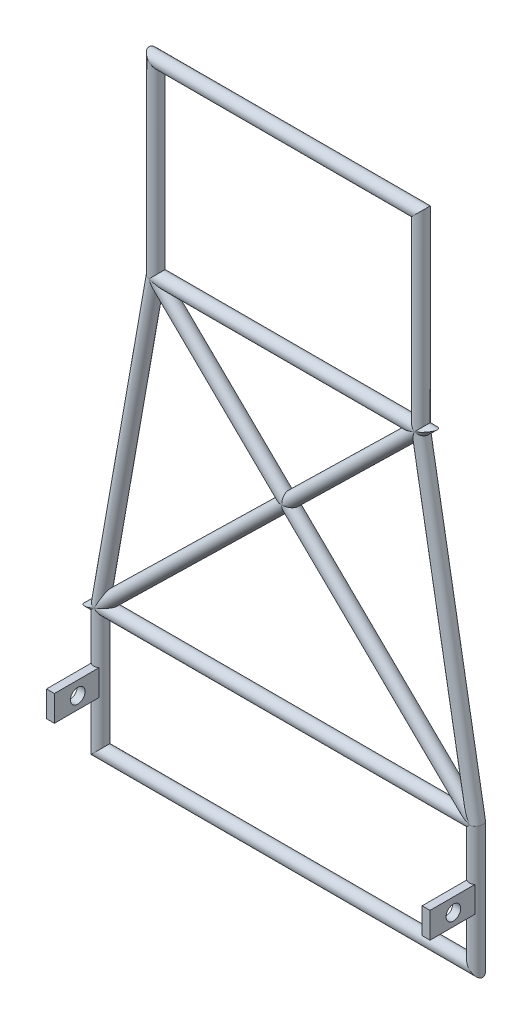
SolidWorks part; units mm, degrees
ref_plane "Front Plane" through (0, 0, 0) normal (0, 0, 1) x (1, 0, 0)
ref_plane "Top Plane" through (0, 0, 0) normal (0, 1, 0) x (1, 0, 0)
ref_plane "Right Plane" through (0, 0, 0) normal (1, 0, 0) x (0, 0, -1)
sketch "Sketch1" plane through (0, 0, 0) normal (0, 0, 1) x (1, 0, 0)
  line L0 (-211.8365, 700) -> (211.8365, 700)
  line L1 (-300, 0) -> (300, 0)
  line L2 (300, 0) -> (300, 200)
  line L3 (-300, 200) -> (211.8365, 700)
  line L4 (300, 200) -> (211.8365, 700)
  line L5 (211.8365, 700) -> (211.8365, 1000)
  line L6 (211.8365, 1000) -> (-211.8365, 1000)
  line L7 (-300, 0) -> (-300, 200)
  line L8 (-300, 200) -> (-211.8365, 700)
  line L9 (-211.8365, 700) -> (-211.8365, 1000)
  line L10 (300, 200) -> (-211.8365, 700)
  line L11 (-300, 200) -> (300, 200)
  dimension "D3" = 200
  dimension "D5" = 300
other "Pipe - configured 21.3 X 2.3(1)"
ref_plane "Plane1" through (-211.8365, 700, 0) normal (0, 1, 0) x (-1, 0, 0)
sketch "Sketch11" plane through (-211.8365, 700, 0) normal (0, 1, 0) x (-1, 0, 0)
  circle A0 centre (0, 0) radius 8.35
  circle A1 centre (0, 0) radius 10.65
  point P3 (0, 10.65)
  point P5 (-10.65, 0)
  point P6 (0, -10.65)
  point P7 (10.65, 0)
  point P8 (0, 0)
  dimension "In_dia" = 16.7
  dimension "Out_dia" = 21.3
other "Pipe - configured 21.3 X 2.3(2)"
ref_plane "Plane2" through (-211.8365, 700, 0) normal (1, 0, 0) x (0, 1, 0)
sketch "Sketch12" plane through (-211.8365, 700, 0) normal (1, 0, 0) x (0, 1, 0)
  circle A0 centre (0, 0) radius 8.35
  circle A1 centre (0, 0) radius 10.65
  point P3 (0, 10.65)
  point P5 (-10.65, 0)
  point P6 (0, -10.65)
  point P7 (10.65, 0)
  point P8 (0, 0)
  dimension "In_dia" = 16.7
  dimension "Out_dia" = 21.3
other "Pipe - configured 21.3 X 2.3(3)"
ref_plane "Plane3" through (300, 200, 0) normal (-0.7153, 0.6988, 0) x (-0.6988, -0.7153, 0)
sketch "Sketch13" plane through (300, 200, 0) normal (-0.7153, 0.6988, 0) x (-0.6988, -0.7153, 0)
  circle A0 centre (0, 0) radius 8.35
  circle A1 centre (0, 0) radius 10.65
  point P3 (0, 10.65)
  point P5 (-10.65, 0)
  point P6 (0, -10.65)
  point P7 (10.65, 0)
  point P8 (0, 0)
  dimension "In_dia" = 16.7
  dimension "Out_dia" = 21.3
sketch "Sketch14" plane through (0, 0, 0) normal (0, 0, 1) x (1, 0, 0)
  line L0 (0, 0) -> (0, 305.8859) construction
  line L1 (306.3871, 78.6524) -> (293.747, 78.6524)
  line L2 (-306.3871, 119.9433) -> (-293.747, 119.9433)
  line L3 (-306.3871, 119.9433) -> (-306.3871, 78.6524)
  line L4 (-306.3871, 78.6524) -> (-293.747, 78.6524)
  line L5 (-293.747, 119.9433) -> (-293.747, 78.6524)
  line L6 (306.3871, 119.9433) -> (306.3871, 78.6524)
  line L7 (306.3871, 119.9433) -> (293.747, 119.9433)
  line L8 (293.747, 119.9433) -> (293.747, 78.6524)
extrude "Boss-Extrude1" add sketch "Sketch14" along normal blind 80 separate body
sketch "Sketch16" plane through (-306.3871, 0, 0) normal (-1, 0, 0) x (0, 0, 1)
  circle A0 centre (42.6798, 98.1951) radius 11.6987
extrude "Cut-Extrude1" cut sketch "Sketch16" against normal blind 730
